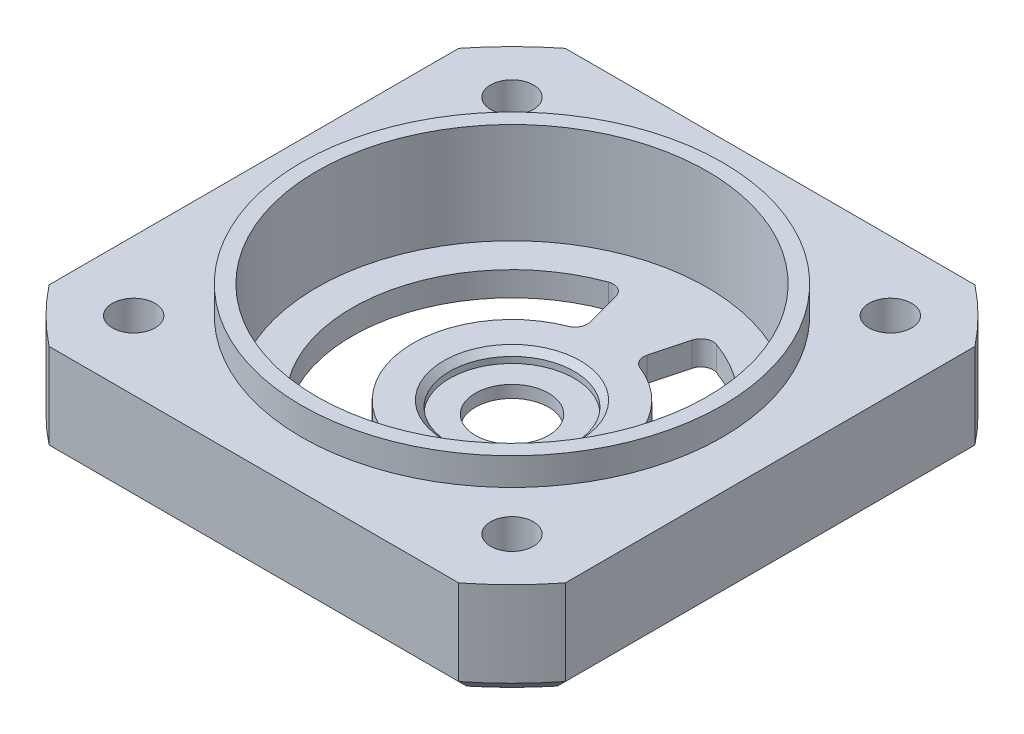
SolidWorks part; units mm, degrees
ref_plane "Front Plane" through (0, 0, 0) normal (0, 0, 1) x (1, 0, 0)
ref_plane "Top Plane" through (0, 0, 0) normal (0, 1, 0) x (1, 0, 0)
ref_plane "Right Plane" through (0, 0, 0) normal (1, 0, 0) x (0, 0, -1)
sketch "Sketch2" plane through (0, 0, 0) normal (0, 1, 0) x (1, 0, 0)
  line L1 (-21.15, 21.15) -> (21.15, 21.15)
  line L2 (-21.15, 21.15) -> (-21.15, -21.15)
  line L3 (-21.15, -21.15) -> (21.15, -21.15)
  line L4 (21.15, 21.15) -> (21.15, -21.15)
  line L5 (-21.15, 21.15) -> (21.15, -21.15) construction
  line L6 (-21.15, -21.15) -> (21.15, 21.15) construction
  point P0 (0, 0)
  dimension "D1" = 42.3
extrude "Boss-Extrude1" add sketch "Sketch2" along normal blind 8
sketch "Sketch5" plane through (0, 8, 0) normal (0, 1, 0) x (1, 0, 0)
  circle A0 centre (0, 0) radius 27
  circle A1 centre (0, 0) radius 29.9106
  dimension "D1" = 54
extrude "Cut-Extrude4" cut sketch "Sketch5" against normal through all
sketch "Sketch6" plane through (0, 8, 0) normal (0, 1, 0) x (1, 0, 0)
  circle A2 centre (0, 0) radius 16
  circle A3 centre (0, 0) radius 10 construction
  dimension "D1" = 32
  dimension "D5" = 20
extrude "Cut-Extrude7" cut sketch "Sketch6" against normal offset from surface (7 mm away) 1 up to face at (0, 0, 0)
sketch "Sketch8" plane through (0, 1, 0) normal (0, 1, 0) x (1, 0, 0)
  circle A0 centre (0, 0) radius 5.1
  circle A2 centre (0, 0) radius 16
  circle A3 centre (0, 0) radius 16
  dimension "D1" = 10.2
  dimension "D2" = 0
extrude "Boss-Extrude3" add sketch "Sketch8" along normal blind 1
sketch "Sketch9" plane through (0, 2, 0) normal (0, 1, 0) x (1, 0, 0)
  line L0 (3.3905, 12.6536) -> (2.0964, 7.824)
  line L1 (3.3905, -12.6536) -> (2.0964, -7.824)
  line L2 (2.0964, -7.824) -> (0, 0) construction
  line L3 (2.0964, 7.824) -> (0, 0) construction
  line L4 (-21.15, 16.7833) -> (-21.15, -16.7833) construction
  line L5 (0, -4.4) -> (0, 4.4) construction
  line L6 (-2.0964, 7.824) -> (0, 0) construction
  line L7 (-2.0964, -7.824) -> (0, 0) construction
  line L8 (-3.3905, -12.6536) -> (-2.0964, -7.824)
  line L9 (-3.3905, 12.6536) -> (-2.0964, 7.824)
  arc A0 (3.3905, 12.6536) -> (3.3905, -12.6536) centre (0, 0) cw
  circle A1 centre (0, 0) radius 5.1 construction
  arc A2 (2.0964, 7.824) -> (2.0964, -7.824) centre (0, 0) cw
  arc A3 (-2.0964, 7.824) -> (-2.0964, -7.824) centre (0, 0) ccw
  arc A4 (-3.3905, 12.6536) -> (-3.3905, -12.6536) centre (0, 0) ccw
  dimension "D1" = 15
  dimension "D4" = 3
  dimension "D2" = 15
  dimension "D3" = 5
extrude "Cut-Extrude8" cut sketch "Sketch9" against normal through all
fillet "Fillet1" radius 1 8 edges at (-3.3905, 1, 12.6536) (-2.0964, 1, -7.824) (-2.0964, 1, 7.824) (-3.3905, 1, -12.6536) (2.0964, 1, 7.824) (2.0964, 1, -7.824) (3.3905, 1, 12.6536) (3.3905, 1, -12.6536)
sketch "Sketch10" plane through (0, 1, 0) normal (0, 1, 0) x (1, 0, 0)
  circle A0 centre (0, 0) radius 3
  dimension "D1" = 6
extrude "Cut-Extrude9" cut sketch "Sketch10" against normal through all
sketch "Sketch7" plane through (0, 8, 0) normal (0, 1, 0) x (1, 0, 0)
  line L1 (-15.5, 15.5) -> (15.5, 15.5) construction
  line L2 (-15.5, 15.5) -> (-15.5, -15.5) construction
  line L3 (-15.5, -15.5) -> (15.5, -15.5) construction
  line L4 (15.5, 15.5) -> (15.5, -15.5) construction
  line L5 (-15.5, 15.5) -> (15.5, -15.5) construction
  line L6 (-15.5, -15.5) -> (15.5, 15.5) construction
  circle A0 centre (-15.5, 15.5) radius 1.75
  circle A1 centre (15.5, 15.5) radius 1.75
  circle A2 centre (15.5, -15.5) radius 1.75
  circle A3 centre (-15.5, -15.5) radius 1.75
  point P0 (0, 0)
  point P16 (0, 0)
  dimension "D3" = 3.5
  dimension "D1" = 31
  dimension "D2" = 31
  dimension "D4" = 4
extrude "Cut-Extrude6" cut sketch "Sketch7" against normal through all
chamfer "Chamfer4" distance 1 angle 45 8 edges at (19.0919, 0, 19.0919) (0, 0, 21.15) (-19.0919, 0, 19.0919) (-21.15, 0, 0) (-19.0919, 0, -19.0919) (0, 0, -21.15) (19.0919, 0, -19.0919) (21.15, 0, 0)
chamfer "Chamfer5" distance 2 angle 45 4 edges at (-15.5, 0, -13.75) (15.5, 0, -13.75) (15.5, 0, 17.25) (-15.5, 0, 17.25)
chamfer "Chamfer6" distance 0.5 angle 45 1 edges at (0, 2, 5.1)
sketch "Sketch11" plane through (0, 8, 0) normal (0, 1, 0) x (1, 0, 0)
  circle A1 centre (0, 0) radius 16 construction
  circle A2 centre (0, 0) radius 16
  circle A3 centre (0, 0) radius 17.25
  dimension "D1" = 1.25
extrude "Boss-Extrude4" add sketch "Sketch11" along normal blind 2.25
